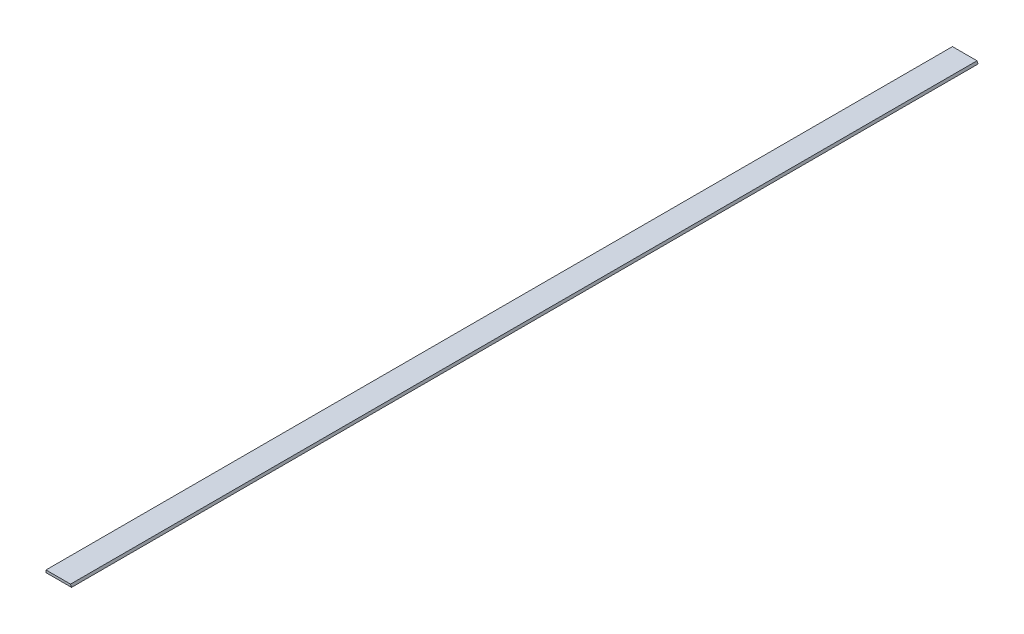
SolidWorks part; units mm, degrees
ref_plane "Front Plane" through (0, 0, 0) normal (0, 0, 1) x (1, 0, 0)
ref_plane "Top Plane" through (0, 0, 0) normal (0, 1, 0) x (1, 0, 0)
ref_plane "Right Plane" through (0, 0, 0) normal (1, 0, 0) x (0, 0, -1)
sketch "Sketch1" plane through (0, 0, 0) normal (0, 0, 1) x (1, 0, 0)
  line L0 (0, 0) -> (0, 2.3622)
  line L1 (0, 2.3622) -> (24.4215, 2.3622)
  line L2 (24.4215, 2.3622) -> (25.4, 0)
  line L3 (25.4, 0) -> (0, 0)
  dimension "D1" = 67.5
  dimension "D2" = 25.4
  dimension "D3" = 2.3622
extrude "Boss-Extrude1" add sketch "Sketch1" along normal blind 901.7
